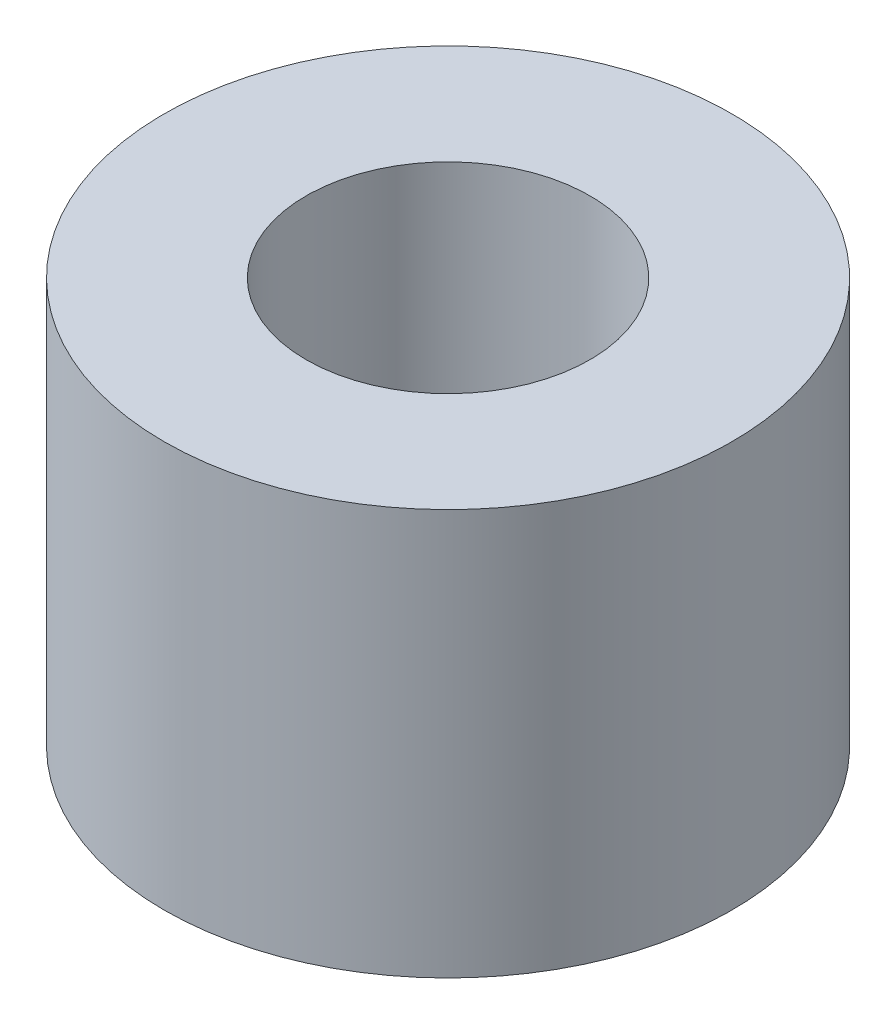
SolidWorks part; units mm, degrees
ref_plane "Front Plane" through (0, 0, 0) normal (0, 0, 1) x (1, 0, 0)
ref_plane "Top Plane" through (0, 0, 0) normal (0, 1, 0) x (1, 0, 0)
ref_plane "Right Plane" through (0, 0, 0) normal (1, 0, 0) x (0, 0, -1)
sketch "Sketch1" plane through (0, 0, 0) normal (0, 1, 0) x (1, 0, 0)
  circle A0 centre (0, 0) radius 1.75
  circle A1 centre (0, 0) radius 3.5
  dimension "D1" = 3.5
  dimension "D2" = 7
extrude "Boss-Extrude1" add sketch "Sketch1" along normal blind 5
